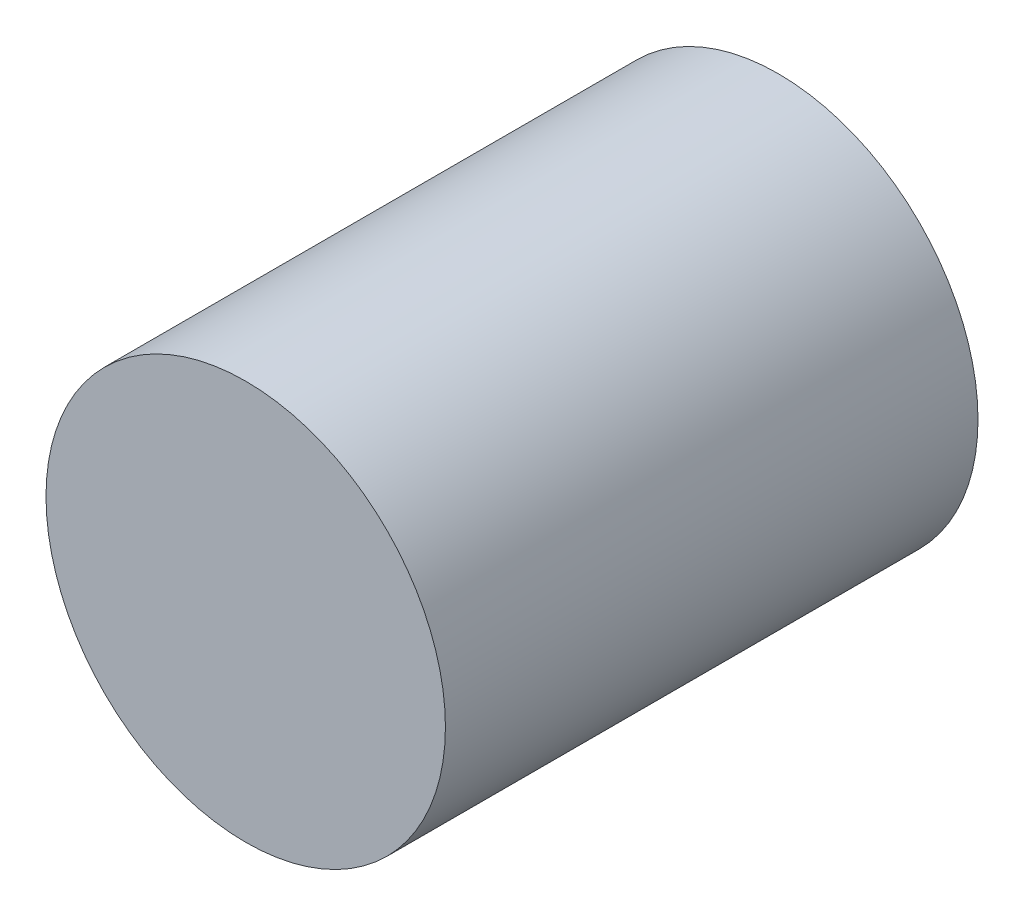
SolidWorks part; units mm, degrees
ref_plane "Plan de face" through (0, 0, 0) normal (0, 0, 1) x (1, 0, 0)
ref_plane "Plan de dessus" through (0, 0, 0) normal (0, 1, 0) x (1, 0, 0)
ref_plane "Plan de droite" through (0, 0, 0) normal (1, 0, 0) x (0, 0, -1)
sketch "Esquisse1" plane through (0, 0, 0) normal (0, 0, 1) x (1, 0, 0)
  circle A0 centre (0, 0) radius 37.5
  dimension "D1" = 75
extrude "Boss.-Extru.1" add sketch "Esquisse1" along normal blind 100
